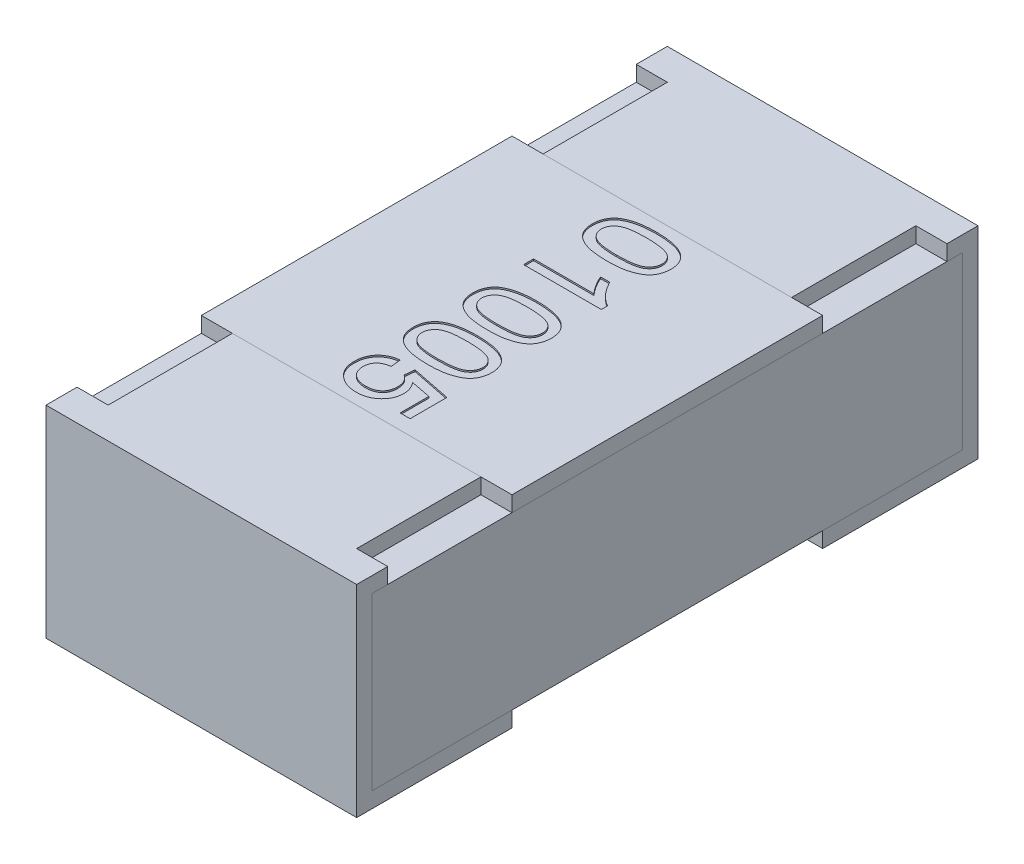
SolidWorks part; units mm, degrees
ref_plane "Front Plane" through (0, 0, 0) normal (0, 0, 1) x (1, 0, 0)
ref_plane "Top Plane" through (0, 0, 0) normal (0, 1, 0) x (1, 0, 0)
ref_plane "Right Plane" through (0, 0, 0) normal (1, 0, 0) x (0, 0, -1)
sketch "Sketch4" plane through (0, 0, 0) normal (1, 0, 0) x (0, 0, -1)
  line L0 (0, 0.1169) -> (0, -0.0721) construction
  line L1 (-0.2, 0) -> (0.3788, 0) construction
  line L2 (-0.2, 0.065) -> (-0.2, -0.065)
  line L3 (-0.2, -0.065) -> (-0.1, -0.065)
  line L4 (-0.1, 0.065) -> (-0.1, 0.055)
  line L5 (-0.1, 0.055) -> (-0.19, 0.055)
  line L6 (-0.19, 0.055) -> (-0.19, -0.055)
  line L7 (-0.19, -0.055) -> (-0.1, -0.055)
  line L8 (-0.1, -0.055) -> (-0.1, -0.065)
  line L9 (-0.1, 0.065) -> (-0.2, 0.065)
  line L10 (0.1, 0.065) -> (0.2, 0.065)
  line L11 (0.1, -0.055) -> (0.1, -0.065)
  line L12 (0.19, -0.055) -> (0.1, -0.055)
  line L13 (0.19, 0.055) -> (0.19, -0.055)
  line L14 (0.1, 0.055) -> (0.19, 0.055)
  line L15 (0.1, 0.065) -> (0.1, 0.055)
  line L16 (0.2, -0.065) -> (0.1, -0.065)
  line L17 (0.2, 0.065) -> (0.2, -0.065)
  dimension "LENGTH" = 0.2
  dimension "HEIGHT" = 0.13
  dimension "END CAP TOP LENGTH" = 0.1
  dimension "END CAP BOTTOM LENGTH" = 0.1
  dimension "D5" = 0.01
  dimension "D6" = 0.01
extrude "Boss-Extrude2" add sketch "Sketch4" along normal mid plane 0.2
sketch "Sketch5" plane through (0, 0, 0) normal (1, 0, 0) x (0, 0, -1)
  line L1 (-0.19, 0.055) -> (0.19, 0.055)
  line L2 (-0.19, 0.055) -> (-0.19, -0.055)
  line L3 (-0.19, -0.055) -> (0.19, -0.055)
  line L4 (0.19, 0.055) -> (0.19, -0.055)
extrude "Boss-Extrude3" add sketch "Sketch5" along normal up to surface and the other way up to surface separate body
sketch "Sketch6" plane through (0, 0.065, 0) normal (0, 1, 0) x (1, 0, 0)
  line L0 (-0.1, 0.2) -> (-0.1, 0.1) construction
  line L1 (-0.1, 0.18) -> (-0.08, 0.18)
  line L2 (-0.1, 0.18) -> (-0.1, 0.1)
  line L3 (-0.1, 0.1) -> (-0.08, 0.1)
  line L4 (-0.08, 0.18) -> (-0.08, 0.1)
  line L5 (0.1, 0.1) -> (-0.1, 0.1) construction
  line L6 (0, 0.0345) -> (0, -0.0345) construction
  line L7 (-0.0325, 0) -> (0.03, 0) construction
  line L8 (0.1, 0.18) -> (0.1, 0.1)
  line L9 (0.1, 0.1) -> (0.08, 0.1)
  line L10 (0.08, 0.18) -> (0.08, 0.1)
  line L11 (0.1, 0.18) -> (0.08, 0.18)
  line L12 (0.1, -0.18) -> (0.08, -0.18)
  line L13 (0.1, -0.18) -> (0.1, -0.1)
  line L14 (0.1, -0.1) -> (0.08, -0.1)
  line L15 (0.08, -0.18) -> (0.08, -0.1)
  line L16 (-0.1, -0.18) -> (-0.08, -0.18)
  line L17 (-0.1, -0.18) -> (-0.1, -0.1)
  line L18 (-0.1, -0.1) -> (-0.08, -0.1)
  line L19 (-0.08, -0.18) -> (-0.08, -0.1)
  dimension "TOP CUT WIDTH" = 0.02
  dimension "TOP CUT LENGTH" = 0.08
extrude "Cut-Extrude1" cut sketch "Sketch6" against normal up to surface (0.01 mm away) up to face at (0, 0.055, 0)
sketch "Sketch7" plane through (0, 0.055, 0) normal (0, 1, 0) x (1, 0, 0)
  line L1 (-0.1, 0.1) -> (0.1, 0.1)
  line L2 (-0.1, 0.1) -> (-0.1, -0.1)
  line L3 (-0.1, -0.1) -> (0.1, -0.1)
  line L4 (0.1, 0.1) -> (0.1, -0.1)
  line L5 (0.08, -0.1) -> (-0.08, -0.1) construction
  line L6 (0.08, 0.1) -> (-0.08, 0.1) construction
  line L7 (-0.1, -0.19) -> (-0.1, 0.19) construction
  line L8 (0.1, 0.19) -> (0.1, -0.19) construction
extrude "Boss-Extrude4" add sketch "Sketch7" along normal up to surface (0.01 mm away) separate body up to face at (0, 0.065, -0.165)
sketch "PART NUMBER" plane through (0, 0.065, 0) normal (0, 1, 0) x (1, 0, 0)
  line L0 (-0.0246, 0.1) -> (-0.0246, -0.1) construction
  line L1 (0, 0) -> (-0.0246, 0) construction
  text T0 "01005" font "Arial" height 0.05
  dimension "D1" = 0.2
extrude "TEXT01005" cut sketch "PART NUMBER" against normal blind 0.001
